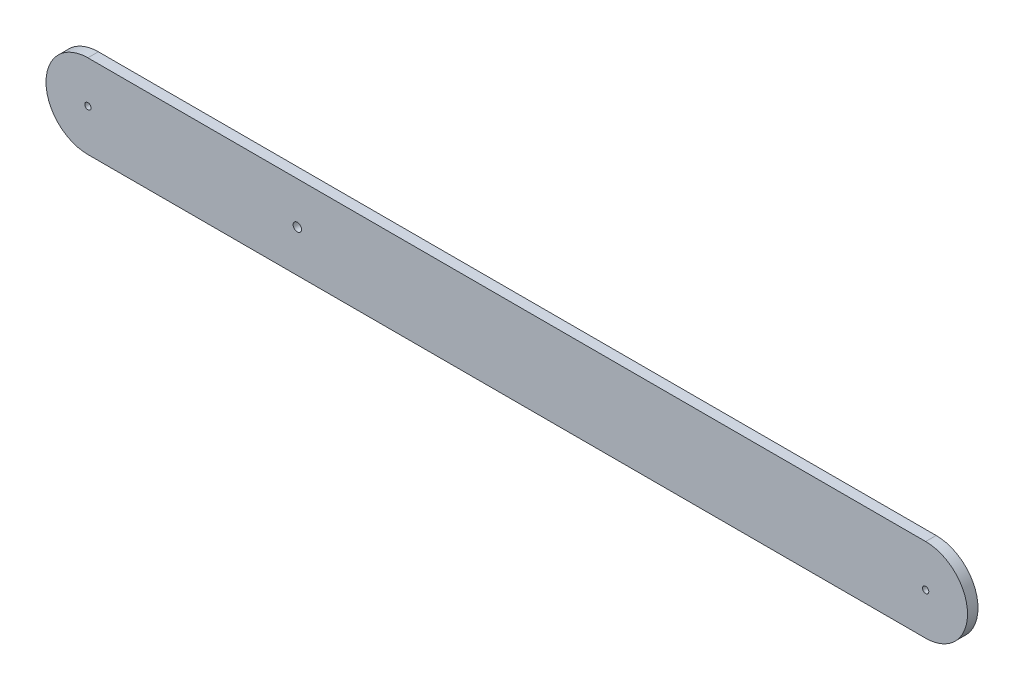
SolidWorks part; units mm, degrees
ref_plane "Front Plane" through (0, 0, 0) normal (0, 0, 1) x (1, 0, 0)
ref_plane "Top Plane" through (0, 0, 0) normal (0, 1, 0) x (1, 0, 0)
ref_plane "Right Plane" through (0, 0, 0) normal (1, 0, 0) x (0, 0, -1)
sketch "Sketch1" plane through (0, 0, 0) normal (0, 0, 1) x (1, 0, 0)
  line L0 (-192.4466, 0) -> (207.5534, 0) construction
  line L1 (-192.4466, 20) -> (207.5534, 20)
  line L2 (-192.4466, -20) -> (207.5534, -20)
  arc A0 (-192.4466, 20) -> (-192.4466, -20) centre (-192.4466, 0) ccw
  arc A1 (207.5534, -20) -> (207.5534, 20) centre (207.5534, 0) ccw
  circle A2 centre (-192.4466, 0) radius 1.5
  circle A3 centre (207.5534, 0) radius 1.5
  circle A4 centre (-92.4466, 0) radius 2
  point P3 (7.5534, 0)
  dimension "D3" = 3
  dimension "D5" = 4
  dimension "D6" = 3
  dimension "D1" = 400
  dimension "D2" = 40
  dimension "D4" = 100
extrude "Boss-Extrude1" add sketch "Sketch1" along normal blind 5
